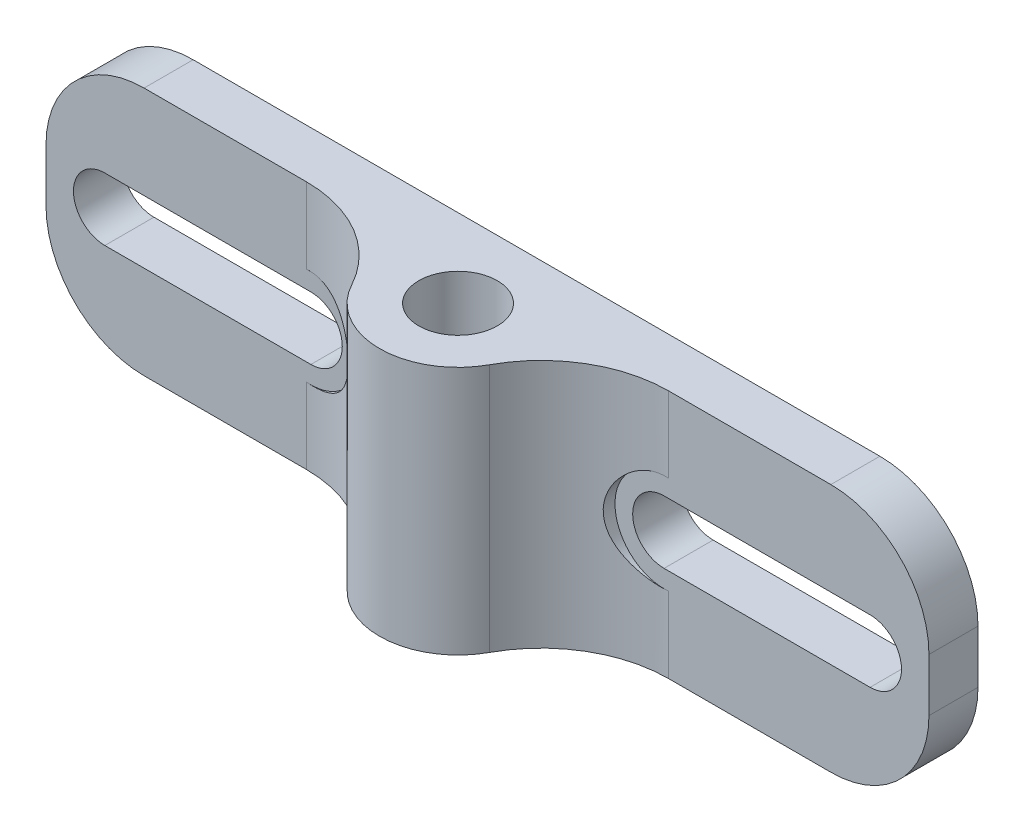
SolidWorks part; units mm, degrees
ref_plane "Front Plane" through (0, 0, 0) normal (0, 0, 1) x (1, 0, 0)
ref_plane "Top Plane" through (0, 0, 0) normal (0, 1, 0) x (1, 0, 0)
ref_plane "Right Plane" through (0, 0, 0) normal (1, 0, 0) x (0, 0, -1)
sketch "Sketch1" plane through (0, 0, 0) normal (0, 1, 0) x (1, 0, 0)
  line L0 (-45, 0) -> (45, 0)
  line L1 (0, 0) -> (0, -8) construction
  line L2 (-45, 0) -> (-45, -5)
  line L3 (-45, -5) -> (-7.4162, -5)
  line L4 (45, -5) -> (7.4162, -5)
  line L5 (45, 0) -> (45, -5)
  circle A0 centre (0, -8) radius 4
  circle A1 centre (0, -8) radius 8 construction
  arc A2 (-7.4162, -5) -> (7.4162, -5) centre (0, -8) ccw
  point P4 (0, 0)
  dimension "D2" = 8
  dimension "D4" = 16
  dimension "D1" = 90
  dimension "D3" = 8
  dimension "D5" = 5
extrude "Boss-Extrude1" add sketch "Sketch1" along normal blind 25.4
fillet "Fillet1" radius 13 2 edges at (7.4162, 12.7, 5) (-7.4162, 12.7, 5)
sketch "Sketch2" plane through (0, 0, 5) normal (0, 0, 1) x (1, 0, 0)
  line L0 (-45, 12.7) -> (45, 12.7) construction
  line L1 (-45, 25.4) -> (-45, 0) construction
  line L2 (45, 25.4) -> (45, 0) construction
  line L3 (-39, 15.9) -> (-18, 15.9)
  line L4 (-39, 9.5) -> (-18, 9.5)
  line L5 (0, 0) -> (0, -12.4562) construction
  line L6 (39, 9.5) -> (18, 9.5)
  line L7 (39, 15.9) -> (18, 15.9)
  circle A0 centre (-39, 12.7) radius 3.2 construction
  circle A1 centre (-18, 12.7) radius 3.2 construction
  arc A2 (-18, 15.9) -> (-18, 9.5) centre (-18, 12.7) cw
  arc A3 (-39, 15.9) -> (-39, 9.5) centre (-39, 12.7) ccw
  circle A4 centre (18, 12.7) radius 3.2 construction
  circle A5 centre (39, 12.7) radius 3.2 construction
  arc A6 (39, 15.9) -> (39, 9.5) centre (39, 12.7) cw
  arc A7 (18, 15.9) -> (18, 9.5) centre (18, 12.7) ccw
  dimension "D1" = 6.4
  dimension "D2" = 21
  dimension "D3" = 6
extrude "Cut-Extrude1" cut sketch "Sketch2" against normal through all both and the other way through all
sketch "Sketch3" plane through (0, 0, 5) normal (0, 0, 1) x (1, 0, 0)
  circle A0 centre (-18, 12.7) radius 5
  circle A1 centre (18, 12.7) radius 5
  dimension "D1" = 10
  dimension "D2" = 10
extrude "Cut-Extrude2" cut sketch "Sketch3" along normal blind 25.4
fillet "Fillet2" radius 10 4 edges at (-45, 25.4, 2.5) (-45, 0, 2.5) (45, 0, 2.5) (45, 25.4, 2.5)
